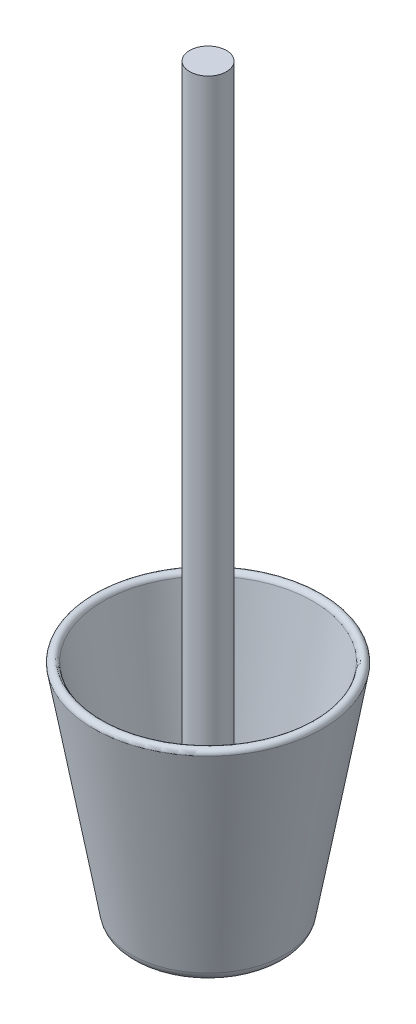
SolidWorks part; units mm, degrees
material "Ceramic Porcelain"
ref_plane "Front Plane" through (0, 0, 0) normal (0, 0, 1) x (1, 0, 0)
ref_plane "Top Plane" through (0, 0, 0) normal (0, 1, 0) x (1, 0, 0)
ref_plane "Right Plane" through (0, 0, 0) normal (1, 0, 0) x (0, 0, -1)
sketch "Sketch1" plane through (0, 0, 0) normal (0, 0, 1) x (1, 0, 0)
  line L0 (0, 0) -> (44.1396, 0)
  line L1 (51.9566, 6.5592) -> (77.6722, 152.4)
  line L2 (0, 0) -> (0, 198.0077) construction
  line L3 (50.8, 0) -> (50.8, 198.0077) construction
  line L4 (0, 6.35) -> (44.1396, 6.35)
  line L5 (45.703, 7.6618) -> (71.3222, 152.9556)
  line L6 (0, 6.35) -> (0, 0)
  line L7 (45.703, 7.6618) -> (71.4187, 153.5027) construction
  line L8 (0, 6.35) -> (44.1396, 6.35) construction
  arc A0 (44.1396, 0) -> (51.9566, 6.5592) centre (44.1396, 7.9375) ccw
  arc A1 (71.3222, 152.9556) -> (77.6722, 152.4) centre (74.4729, 152.4) cw
  arc A2 (45.703, 7.6618) -> (44.1396, 6.35) centre (44.1396, 7.9375) cw
  arc A3 (44.1396, 6.35) -> (45.703, 7.6618) centre (44.1396, 7.9375) ccw construction
  dimension "Base Outer Radius" = 7.9375
  dimension "Base Inner Radius" = 1.5875
  dimension "Wall Height" = 152.4
  dimension "Wall Angle" = 10
  dimension "Base Dia" = 101.6
  dimension "Wall Thickness" = 6.35
revolve "Revolve1" add sketch "Sketch1" angle 360 about L2
sketch "Esquisse1" plane through (0, 6.35, 0) normal (0, 1, 0) x (1, 0, 0)
  circle A0 centre (0, 0) radius 12.5
  dimension "D1" = 25
extrude "Boss.-Extru.2" add sketch "Esquisse1" along normal blind 500
equation "\"Wall Height@Sketch1\" = 1.5*\"Base Dia@Sketch1\""
equation "\"Base Outer Radius@Sketch1\" = 1.25*\"Wall Thickness@Sketch1\""
equation "\"Base Inner Radius@Sketch1\" = \"Base Outer Radius@Sketch1\" - \"Wall Thickness@Sketch1\""
equation "\"Wall Thickness@Sketch1\" = .0625 * \"Base Dia@Sketch1\""
